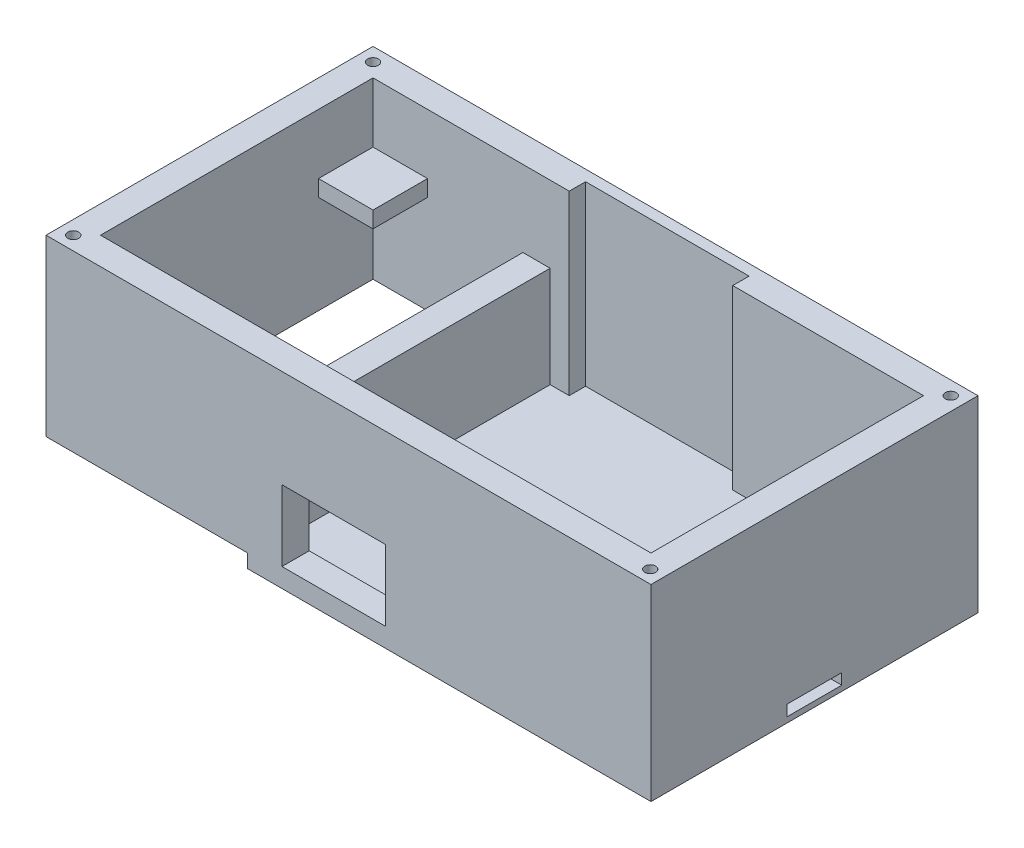
SolidWorks part; units mm, degrees
ref_plane "Front Plane" through (0, 0, 0) normal (0, 0, 1) x (1, 0, 0)
ref_plane "Top Plane" through (0, 0, 0) normal (0, 1, 0) x (1, 0, 0)
ref_plane "Right Plane" through (0, 0, 0) normal (1, 0, 0) x (0, 0, -1)
sketch "Sketch1" plane through (0, 0, 0) normal (0, 1, 0) x (1, 0, 0)
  line L1 (0, 0) -> (111, 0)
  line L2 (0, 0) -> (0, 60)
  line L3 (0, 60) -> (111, 60)
  line L4 (111, 0) -> (111, 60)
  dimension "D1" = 111
  dimension "D2" = 60
extrude "Boss-Extrude1" add sketch "Sketch1" along normal blind 34.5
sketch "Sketch2" plane through (0, 34.5, 0) normal (0, 1, 0) x (1, 0, 0)
  line L0 (55.5, 60) -> (55.5, 0) construction
  line L1 (111, 60) -> (0, 60) construction
  line L2 (0, 0) -> (111, 0) construction
  line L3 (0, 30) -> (111, 30) construction
  line L4 (0, 60) -> (0, 0) construction
  line L5 (111, 0) -> (111, 60) construction
  line L7 (5, 5) -> (106, 5)
  line L8 (5, 5) -> (5, 55)
  line L9 (5, 55) -> (106, 55)
  line L10 (106, 5) -> (106, 55)
  dimension "D1" = 5
  dimension "D2" = 5
  dimension "D3" = 5
  dimension "D4" = 5
  dimension "D5" = 50
  dimension "D6" = 101
extrude "Cut-Extrude1" cut sketch "Sketch2" against normal blind 11
sketch "Sketch3" plane through (0, 34.5, 0) normal (0, 1, 0) x (1, 0, 0)
  line L0 (5, 45) -> (15, 45)
  line L1 (5, 55) -> (5, 5) construction
  line L2 (15, 45) -> (15, 55)
  line L3 (106, 55) -> (5, 55) construction
  line L4 (15, 55) -> (96, 55)
  line L5 (96, 55) -> (96, 45)
  line L6 (96, 45) -> (106, 45)
  line L7 (106, 5) -> (106, 55) construction
  line L8 (106, 45) -> (106, 15)
  line L9 (106, 5) -> (106, 55) construction
  line L10 (106, 15) -> (96, 15)
  line L11 (96, 15) -> (96, 5)
  line L12 (5, 5) -> (106, 5) construction
  line L13 (96, 5) -> (15, 5)
  line L14 (15, 5) -> (15, 15)
  line L15 (15, 15) -> (5, 15)
  line L16 (5, 55) -> (5, 5) construction
  line L17 (5, 15) -> (5, 45)
  dimension "D1" = 10
  dimension "D2" = 10
  dimension "D3" = 10
  dimension "D4" = 10
  dimension "D5" = 10
  dimension "D6" = 10
  dimension "D7" = 10
  dimension "D8" = 10
extrude "Cut-Extrude3" cut sketch "Sketch3" against normal blind 14
sketch "Sketch5" plane through (0, 0, 0) normal (0, -1, 0) x (1, 0, 0)
  line L1 (5, -5) -> (32.5, -5)
  line L2 (5, -5) -> (5, -55)
  line L3 (5, -55) -> (32.5, -55)
  line L4 (32.5, -5) -> (32.5, -55)
  line L6 (0, 0) -> (111, 0) construction
  line L7 (0, -60) -> (0, 0) construction
  line L14 (111, 0) -> (111, -60) construction
  line L15 (106, -55) -> (37.5, -55)
  line L16 (106, -55) -> (106, -5)
  line L17 (106, -5) -> (37.5, -5)
  line L18 (37.5, -55) -> (37.5, -5)
  line L19 (111, -60) -> (0, -60) construction
  dimension "D1" = 27.5
  dimension "D2" = 50
  dimension "D3" = 5
  dimension "D4" = 5
  dimension "D5" = 5
  dimension "D6" = 5
  dimension "D7" = 5
  dimension "D8" = 5
  dimension "D9" = 5
extrude "Cut-Extrude5" cut sketch "Sketch5" against normal blind 18.5 from offset 2 offset against normal yes
sketch "Sketch6" plane through (0, 0, 0) normal (0, -1, 0) x (1, 0, 0)
  line L0 (0, 0) -> (111, 0) construction
  line L1 (0, -60) -> (37, -60)
  line L2 (0, -60) -> (0, 0)
  line L3 (0, 0) -> (37, 0)
  line L4 (37, -60) -> (37, 0)
  dimension "D1" = 60
  dimension "D2" = 37
extrude "Cut-Extrude6" cut sketch "Sketch6" against normal blind 2.5
sketch "Sketch7" plane through (0, 2.5, 0) normal (0, -1, 0) x (-1, 0, 0)
  line L0 (-37, 0) -> (0, 0) construction
  line L1 (0, 0) -> (0, 60) construction
  line L2 (0, 60) -> (-37, 60) construction
  line L3 (-37, 60) -> (-37, 0) construction
  line L4 (-37, 60) -> (-37, 0) construction
  circle A0 centre (-2.5, 57.5) radius 1
  circle A1 centre (-34.5, 57.5) radius 1
  circle A2 centre (-34.5, 2.5) radius 1
  circle A3 centre (-2.5, 2.5) radius 1
  dimension "D1" = 2
  dimension "D2" = 2
  dimension "D3" = 2
  dimension "D4" = 2
  dimension "D5" = 2.5
  dimension "D6" = 2.5
  dimension "D7" = 2.5
  dimension "D8" = 2.5
  dimension "D9" = 2.5
  dimension "D10" = 2.5
  dimension "D11" = 2.5
  dimension "D12" = 2.5
extrude "Cut-Extrude7" cut sketch "Sketch7" against normal blind 4
sketch "Sketch8" plane through (0, 34.5, 0) normal (0, 1, 0) x (1, 0, 0)
  line L0 (111, 60) -> (0, 60) construction
  line L1 (111, 0) -> (111, 60) construction
  line L2 (0, 60) -> (0, 0) construction
  line L3 (0, 0) -> (111, 0) construction
  circle A0 centre (2.5, 57.5) radius 1
  circle A1 centre (108.5, 57.5) radius 1
  circle A2 centre (108.5, 2.3604) radius 1
  circle A3 centre (2.5, 2.5) radius 1
  dimension "D8" = 2
  dimension "D9" = 2
  dimension "D10" = 2
  dimension "D12" = 2
  dimension "D1" = 2.5
  dimension "D2" = 2.5
  dimension "D3" = 2.5
  dimension "D4" = 2.5
  dimension "D5" = 2.5
  dimension "D6" = 2.5
  dimension "D7" = 2.5
  dimension "D11" = 2.5
extrude "Cut-Extrude8" cut sketch "Sketch8" against normal blind 4
sketch "Sketch9" plane through (0, 0, 0) normal (0, 0, 1) x (1, 0, 0)
  line L0 (0, 34.5) -> (111, 34.5) construction
  line L1 (43.2925, 3.5) -> (62.2925, 3.5)
  line L2 (43.2925, 3.5) -> (43.2925, 16.5)
  line L3 (43.2925, 16.5) -> (62.2925, 16.5)
  line L4 (62.2925, 3.5) -> (62.2925, 16.5)
  dimension "D1" = 13
  dimension "D2" = 19
  dimension "D3" = 18
extrude "Cut-Extrude9" cut sketch "Sketch9" against normal blind 10
sketch "Sketch10" plane through (111, 0, 0) normal (1, 0, 0) x (0, 0, -1)
  line L1 (0, 0) -> (60, 0) construction
  line L4 (35, 3) -> (25, 3)
  line L5 (35, 3) -> (35, 1)
  line L6 (35, 1) -> (25, 1)
  line L7 (25, 3) -> (25, 1)
  dimension "D1" = 2
  dimension "D2" = 1
  dimension "D3" = 10
extrude "Cut-Extrude10" cut sketch "Sketch10" against normal blind 70
sketch "Sketch11" plane through (0, 1, 0) normal (0, 1, 0) x (1, 0, 0)
  line L0 (41, 35) -> (106, 35) construction
  line L1 (41, 35) -> (43, 35)
  line L2 (41, 35) -> (41, 25)
  line L3 (41, 25) -> (43, 25)
  line L4 (43, 35) -> (43, 25)
  line L5 (41, 25) -> (41, 35) construction
  dimension "D1" = 2
  dimension "D2" = 10
  dimension "D3" = 0
  dimension "D4" = 0
  dimension "D5" = 2
extrude "Cut-Extrude11" cut sketch "Sketch11" against normal through all
sketch "Sketch12" plane through (0, 34.5, 0) normal (0, 1, 0) x (1, 0, 0)
  line L0 (106, 55) -> (5, 55) construction
  line L1 (71, 55) -> (41, 55)
  line L2 (71, 55) -> (71, 58)
  line L3 (71, 58) -> (41, 58)
  line L4 (41, 55) -> (41, 58)
  line L5 (111, 0) -> (111, 60) construction
  dimension "D1" = 40
  dimension "D2" = 70
  dimension "D3" = 3
  dimension "D4" = 30
extrude "Cut-Extrude12" cut sketch "Sketch12" against normal blind 32.5
